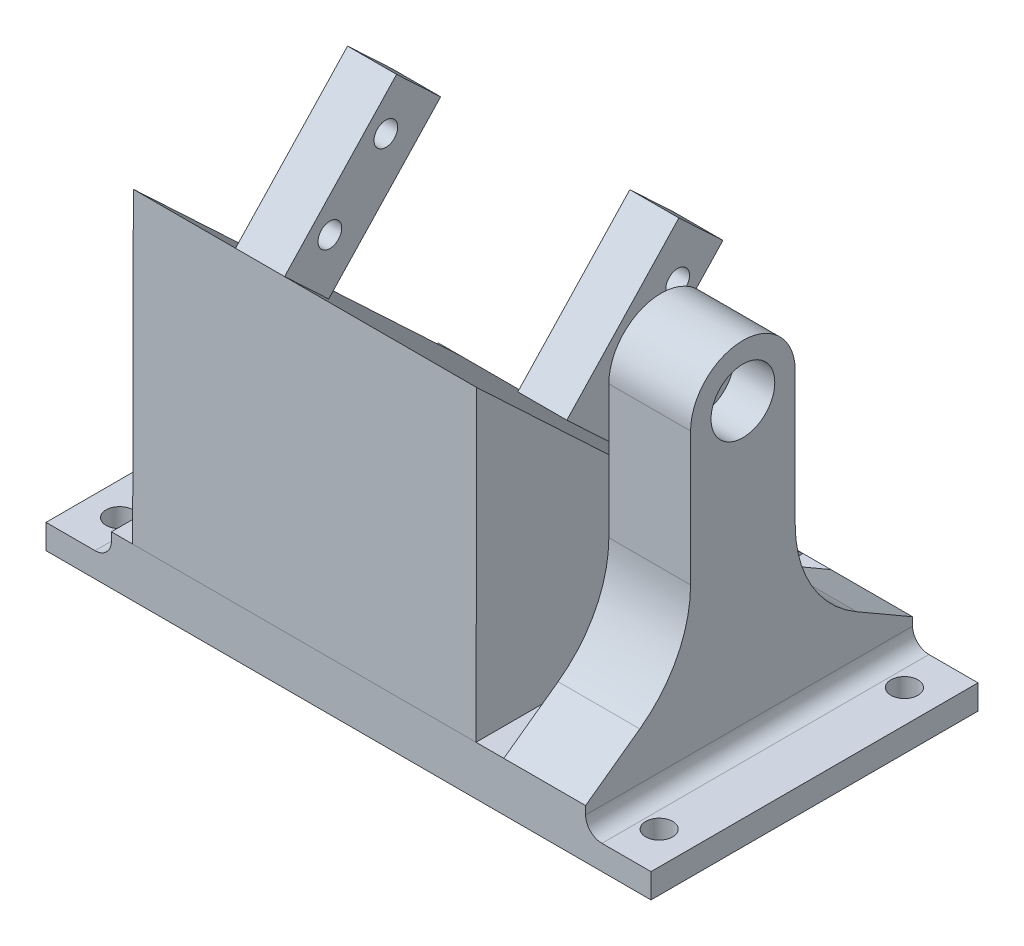
SolidWorks part; units mm, degrees
ref_plane "Front Plane" through (0, 0, 0) normal (0, 0, 1) x (1, 0, 0)
ref_plane "Top Plane" through (0, 0, 0) normal (0, 1, 0) x (1, 0, 0)
ref_plane "Right Plane" through (0, 0, 0) normal (1, 0, 0) x (0, 0, -1)
sketch "Sketch1" plane through (0, 0, 0) normal (0, 1, 0) x (1, 0, 0)
  line L1 (-29, -20) -> (29, -20)
  line L2 (-29, -20) -> (-29, 20)
  line L3 (-29, 20) -> (29, 20)
  line L4 (29, -20) -> (29, 20)
  line L5 (-29, -20) -> (29, 20) construction
  line L6 (-29, 20) -> (29, -20) construction
  point P0 (0, 0)
  dimension "D1" = 58
  dimension "D2" = 40
extrude "Boss-Extrude1" add sketch "Sketch1" along normal blind 6
sketch "Sketch4" plane through (-29, 0, 0) normal (-1, 0, 0) x (0, 0, 1)
  line L0 (-20, 6) -> (19.9186, 43.5439)
  line L1 (96.59, 39.25) -> (-106.2472, 39.25) construction
  line L2 (19.9186, 43.5439) -> (20, 6)
  line L4 (0.7569, 39.25) -> (7.6079, 31.9656) construction
  line L5 (-20, 6) -> (20, 6)
  dimension "D1" = 10
  dimension "D2" = 54.8
  dimension "D3" = 16.9
extrude "Boss-Extrude3" add sketch "Sketch4" against normal blind 42 from offset 2.6 offset against normal yes
sketch "Sketch6" plane through (0, 13.165, -12.3818) normal (0, 0.7284, -0.6851) x (1, 0, 0)
  line L0 (-7.9, -44.3418) -> (-7.9, -36.9418)
  line L1 (15.6, -44.3418) -> (-26.4, -44.3418) construction
  line L2 (-13.9, -36.9418) -> (-13.9, -44.3418)
  line L3 (-26.4, -44.3418) -> (-26.4, 10.4582) construction
  line L4 (15.6, 10.4582) -> (-26.4, 10.4582) construction
  line L5 (-13.9, 10.4582) -> (-7.9, 10.4582)
  line L6 (-13.9, 10.4582) -> (-13.9, 3.0582)
  line L7 (-13.9, 3.0582) -> (-7.9, 3.0582)
  line L8 (-7.9, 10.4582) -> (-7.9, 3.0582)
  line L9 (-13.9, -36.9418) -> (-7.9, -36.9418)
  line L10 (-13.9, -44.3418) -> (-7.9, -44.3418)
  dimension "D1" = 12.5
  dimension "D2" = 6
  dimension "D3" = 7.4
  dimension "D4" = 7.4
extrude "Boss-Extrude4" add sketch "Sketch6" along normal blind 20
sketch "Sketch7" plane through (29, 0, 0) normal (1, 0, 0) x (0, 0, -1)
  line L0 (-20, 6) -> (-13.3646, 10.8004)
  line L1 (-7.1569, 22.9535) -> (-7.1569, 39.25)
  line L2 (5.6431, 39.25) -> (5.6431, 22.9535)
  line L3 (13.1371, 9.9666) -> (20, 6)
  line L4 (-20, 6) -> (20, 6)
  arc A0 (5.6431, 39.25) -> (-7.1569, 39.25) centre (-0.7569, 39.25) ccw
  arc A1 (5.6431, 22.9535) -> (13.1371, 9.9666) centre (20.6431, 22.9535) ccw
  arc A2 (-13.3646, 10.8004) -> (-7.1569, 22.9535) centre (-22.1569, 22.9535) ccw
  dimension "D1" = 12.8
  dimension "D2" = 15
extrude "Boss-Extrude5" add sketch "Sketch7" against normal blind 10
sketch "Sketch8" plane through (29, 0, 0) normal (1, 0, 0) x (0, 0, -1)
  circle A0 centre (-0.7569, 39.25) radius 3.9
  dimension "D1" = 7.8
hole_wizard "M2.5 Clearance Slot1" positions "Sketch9" profile "Sketch10" size "M2.5" standard "ANSI Metric"
sketch "Sketch9" plane through (-16.9, -75.0526, -128.7041) normal (-1, 0, 0) x (0, -0.3807, 0.9247)
  point P0 (57.1895, 125.1689)
  point P2 (66.2981, 121.0417)
  point P4 (77.4128, 169.8009)
  point P6 (86.5214, 165.6737)
sketch "Sketch10" plane through (-16.9, 18.9134, -28.1641) normal (0, 1, 0) x (0, 0, 1)
  line L0 (0, 0) -> (0, 9.8702)
  line L1 (0, 9.8702) -> (1.45, 8.999)
  line L2 (1.45, 8.999) -> (1.45, 0)
  line L3 (1.45, 0) -> (0, 0)
  line L4 (0, 9.8702) -> (-1.45, 8.999) construction
  line L5 (0, -6.35) -> (0, 107.95) construction
  dimension "Hole Dia." = 2.9
  dimension "Hole Depth" = 8.999
  dimension "Drill Angle" = 118
sketch "Sketch11" plane through (29, 0, 0) normal (1, 0, 0) x (0, 0, -1)
  circle A0 centre (-0.7569, 39.25) radius 1.75
  dimension "D1" = 3.5
extrude "Cut-Extrude1" cut sketch "Sketch11" against normal blind 10
sketch "Sketch12" plane through (0, 0, 0) normal (0, 1, 0) x (1, 0, 0)
  line L0 (29, -20) -> (37, -20)
  line L1 (37, -20) -> (37, 20)
  line L2 (37, 20) -> (29, 20)
  line L3 (29, -20) -> (29, 20)
  line L4 (0, -48.6712) -> (0, 87.7762) construction
  line L5 (-29, -20) -> (-29, 20)
  line L6 (-37, 20) -> (-29, 20)
  line L7 (-37, -20) -> (-37, 20)
  line L8 (-29, -20) -> (-37, -20)
  circle A0 centre (33, -15) radius 1.65
  circle A1 centre (33, 15) radius 1.65
  circle A2 centre (-33, 15) radius 1.65
  circle A3 centre (-33, -15) radius 1.65
  dimension "D2" = 4
  dimension "D4" = 3.3
  dimension "D1" = 8
  dimension "D3" = 4
  dimension "D5" = 5
  dimension "D6" = 5
extrude "Boss-Extrude6" add sketch "Sketch12" along normal blind 3
fillet "Fillet1" radius 2 2 edges at (29, 3, 0) (-29, 3, 0)
extrude "Cut-Extrude2" cut sketch "Sketch8" against normal blind 5 contours A0
